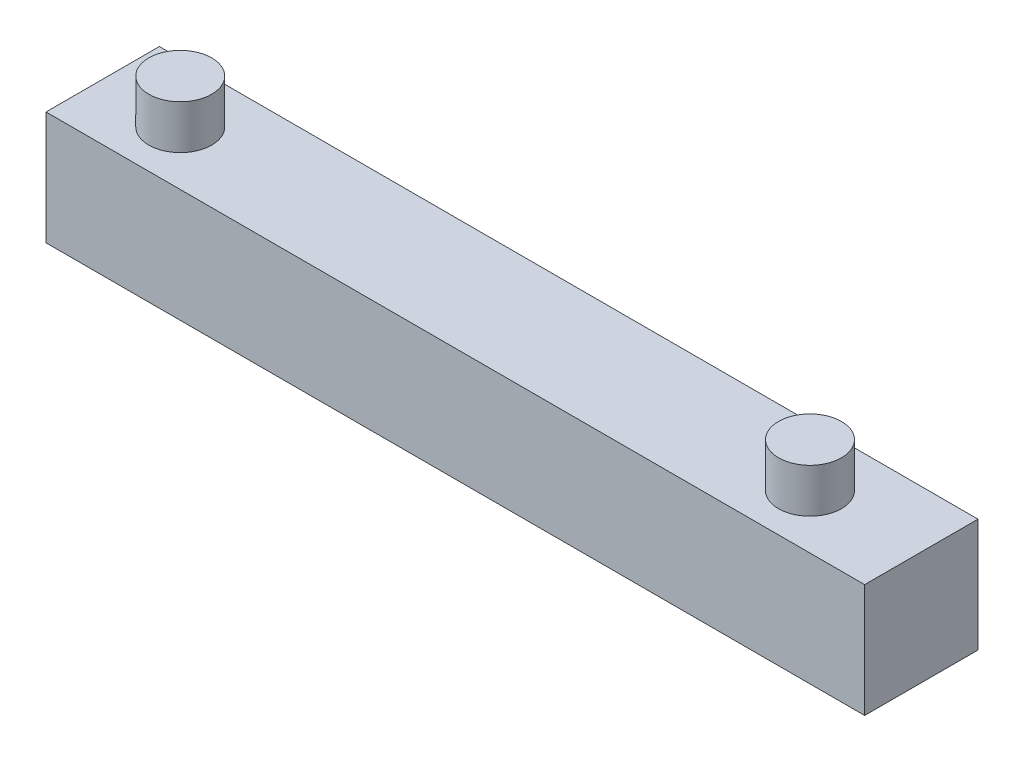
SolidWorks part; units mm, degrees
ref_plane "Front Plane" through (0, 0, 0) normal (0, 0, 1) x (1, 0, 0)
ref_plane "Top Plane" through (0, 0, 0) normal (0, 1, 0) x (1, 0, 0)
ref_plane "Right Plane" through (0, 0, 0) normal (1, 0, 0) x (0, 0, -1)
sketch "Sketch1" plane through (0, 0, 0) normal (0, 0, 1) x (1, 0, 0)
  line L1 (0, 0) -> (650, 0)
  line L2 (0, 0) -> (0, 90)
  line L3 (0, 90) -> (650, 90)
  line L4 (650, 0) -> (650, 90)
  dimension "D1" = 650
  dimension "D2" = 90
extrude "Boss-Extrude1" add sketch "Sketch1" along normal blind 90
sketch "Sketch2" plane through (0, 90, 0) normal (0, 1, 0) x (1, 0, 0)
  circle A0 centre (63.6084, -47.0107) radius 25
  circle A1 centre (563.6084, -47.0107) radius 25
  dimension "D2" = 50
  dimension "D3" = 50
  dimension "D1" = 500
extrude "Boss-Extrude2" add sketch "Sketch2" along normal blind 35
